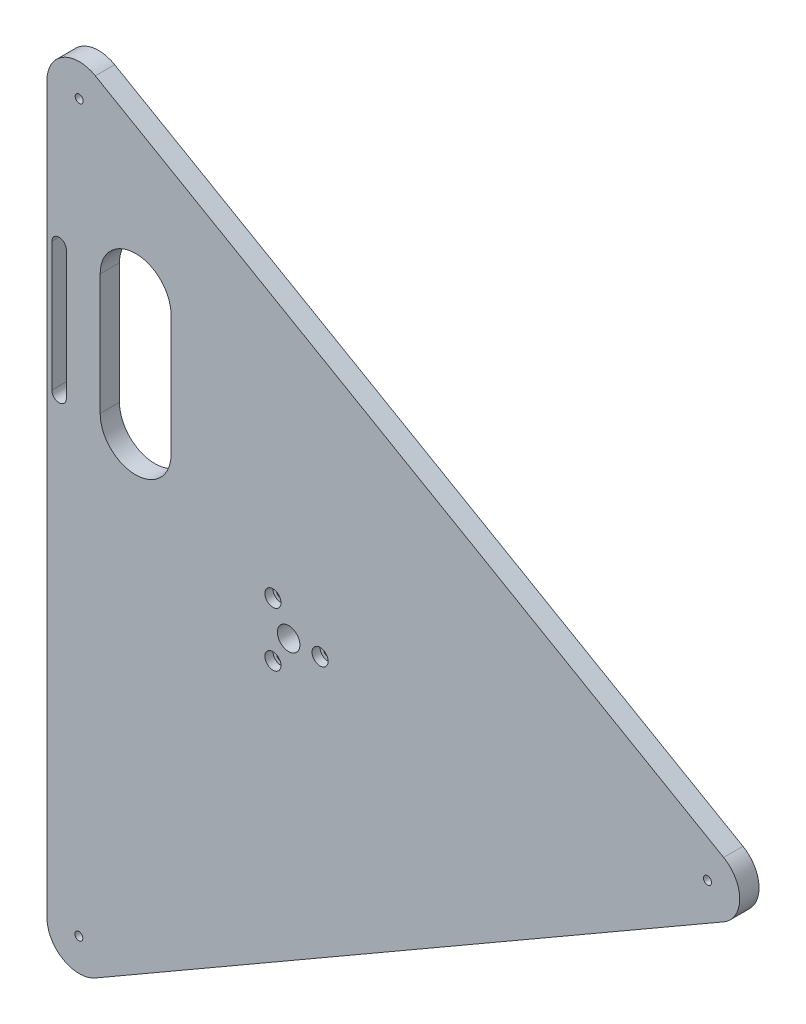
SolidWorks part; units mm, degrees
material "3.1325 (EN-AW 2017A)"
ref_plane "Plan de face" through (0, 0, 0) normal (0, 0, 1) x (1, 0, 0)
ref_plane "Plan de dessus" through (0, 0, 0) normal (0, 1, 0) x (1, 0, 0)
ref_plane "Plan de droite" through (0, 0, 0) normal (1, 0, 0) x (0, 0, -1)
sketch "Esquisse1" plane through (0, 0, 0) normal (0, 0, 1) x (1, 0, 0)
  line L1 (270, 17.3205) -> (-120, 242.4871)
  line L2 (-150, 225.1666) -> (-150, -225.1666)
  line L3 (-120, -242.4871) -> (270, -17.3205)
  arc A0 (270, 17.3205) -> (270, -17.3205) centre (260, 0) cw
  circle A1 centre (0, 0) radius 150 construction
  arc A2 (-150, -225.1666) -> (-120, -242.4871) centre (-130, -225.1666) ccw
  arc A3 (-120, 242.4871) -> (-150, 225.1666) centre (-130, 225.1666) ccw
  dimension "D1" = 20
  dimension "D2" = 20
extrude "Boss.-Extru.1" add sketch "Esquisse1" along normal blind 12
hole_wizard "Trou taraudé M61" positions "Esquisse3" profile "Esquisse2" tap size "M6" standard "ISO" end condition through all
sketch "Esquisse3" plane through (0, 0, 0) normal (0, 0, 1) x (1, 0, 0)
  arc A0 (270, -17.3205) -> (270, 17.3205) centre (260, 0) ccw construction
  point P0 (260, 0)
  dimension "D1" = 0
sketch "Esquisse2" plane through (260, 0, 0) normal (1, 0, 0) x (0, 1, 0)
  line L0 (0, 0) -> (0, 12)
  line L1 (0, 12) -> (2.5, 12)
  line L2 (2.5, 12) -> (2.5, 0)
  line L5 (2.5, 0) -> (0, 0)
  line L11 (0, -6.35) -> (0, 107.95) construction
  dimension "Diamètre du trou pour taraudage jusqu'au prochain" = 5
  dimension "Profondeur du trou pour taraudage jusqu'au prochain" = 12
cosmetic thread "Filetage de perçage1" parameters "D2"=6
hole_wizard "Trou taraudé M62" positions "Esquisse7" profile "Esquisse6" tap size "M6" standard "ISO" end condition through all
sketch "Esquisse7" plane through (0, 0, 12) normal (0, 0, 1) x (1, 0, 0)
  point P0 (-130.2663, -225.0837)
  point P1 (-130, 225.1666)
sketch "Esquisse6" plane through (-130.2663, -225.0837, 12) normal (1, 0, 0) x (0, -1, 0)
  line L0 (0, 0) -> (0, 12)
  line L1 (0, 12) -> (2.5, 12)
  line L2 (2.5, 12) -> (2.5, 0)
  line L5 (2.5, 0) -> (0, 0)
  line L11 (0, -6.35) -> (0, 107.95) construction
  dimension "Diamètre du trou pour taraudage jusqu'au prochain" = 5
  dimension "Profondeur du trou pour taraudage jusqu'au prochain" = 12
cosmetic thread "Filetage de perçage2" parameters "D2"=6
cosmetic thread "Filetage de perçage3" parameters "D2"=6
hole_wizard "Chambrage pour vis à tête hexagonale M51" positions "Esquisse10" profile "Esquisse9" counterbore size "M5" standard "ISO" end condition through all
sketch "Esquisse10" plane through (0, 0, 12) normal (0, 0, 1) x (1, 0, 0)
  point P0 (19.5, 0)
  dimension "D1" = 0
  dimension "D2" = 19.5
sketch "Esquisse9" plane through (19.5, 0, 12) normal (1, 0, 0) x (0, -1, 0)
  line L0 (0, 0) -> (0, 12)
  line L1 (0, 12) -> (2.75, 12)
  line L3 (2.75, 12) -> (2.75, 5)
  line L4 (2.75, 5) -> (5, 5)
  line L5 (5, 5) -> (5, 0)
  line L7 (5, 0) -> (0, 0)
  line L11 (0, -6.35) -> (0, 107.95) construction
  dimension "Diamètre du perçage jusqu'au prochain" = 5.5
  dimension "Profondeur du perçage jusqu'au prochain" = 12
  dimension "Diamètre du chambrage" = 10
  dimension "Profondeur du chambrage" = 5
sketch "Esquisse11" plane through (0, 0, 12) normal (0, 0, 1) x (1, 0, 0)
  circle A0 centre (0, 0) radius 7
extrude "Enlèv. mat.-Extru.1" cut sketch "Esquisse11" against normal through all
pattern_circular "Répétition circulaire1" count 3 over 360 about axis through (0, 0, 0) along (0, 0, 1) of "Chambrage pour vis à tête hexagonale M51"
sketch "Esquisse12" plane through (0, 0, 0) normal (0, 0, -1) x (-1, 0, 0)
  circle A0 centre (0, 0) radius 23.25
extrude "Enlèv. mat.-Extru.2" cut sketch "Esquisse12" against normal blind 1
sketch "Esquisse15" plane through (0, 0, 0) normal (0, 0, -1) x (-1, 0, 0)
  line L0 (95, 137.5025) -> (95, 62.4975) construction
  line L1 (117, 137.5025) -> (117, 62.4975)
  line L2 (73, 137.5025) -> (73, 62.4975)
  arc A0 (117, 137.5025) -> (73, 137.5025) centre (95, 137.5025) ccw
  arc A1 (73, 62.4975) -> (117, 62.4975) centre (95, 62.4975) ccw
  point P2 (95, 100)
  dimension "D1" = 95
  dimension "D2" = 100
extrude "Enlèv. mat.-Extru.4" cut sketch "Esquisse15" against normal through all
sketch "Esquisse16" plane through (0, 0, 12) normal (0, 0, 1) x (1, 0, 0)
  line L0 (-142.5, 140) -> (-142.5, 60) construction
  line L1 (-139.9, 140) -> (-139.9, 60)
  line L2 (-145.1, 140) -> (-145.1, 60)
  arc A0 (-139.9, 140) -> (-145.1, 140) centre (-142.5, 140) ccw
  arc A1 (-145.1, 60) -> (-139.9, 60) centre (-142.5, 60) ccw
  point P2 (-142.5, 100)
  dimension "D1" = 40
  dimension "D2" = 47.5
  dimension "D3" = 5.2
extrude "Enlèv. mat.-Extru.5" cut sketch "Esquisse16" against normal through all
sketch "Esquisse17" plane through (0, 0, 12) normal (0, 0, 1) x (1, 0, 0)
  line L0 (-142.5, 140) -> (-142.5, 60) construction
  line L1 (-138, 140) -> (-138, 60)
  line L2 (-147, 140) -> (-147, 60)
  arc A0 (-138, 140) -> (-147, 140) centre (-142.5, 140) ccw
  arc A1 (-147, 60) -> (-138, 60) centre (-142.5, 60) ccw
  point P2 (-142.5, 100)
  dimension "D1" = 9
extrude "Enlèv. mat.-Extru.6" cut sketch "Esquisse17" against normal blind 9
